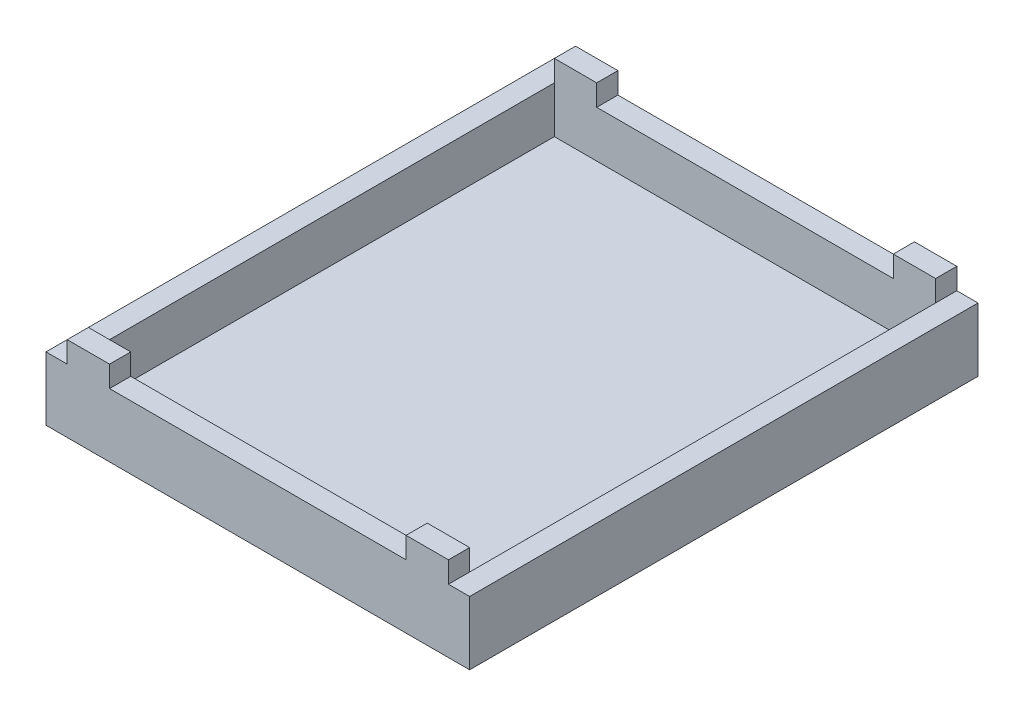
SolidWorks part; units mm, degrees
ref_plane "Front Plane" through (0, 0, 0) normal (0, 0, 1) x (1, 0, 0)
ref_plane "Top Plane" through (0, 0, 0) normal (0, 1, 0) x (1, 0, 0)
ref_plane "Right Plane" through (0, 0, 0) normal (1, 0, 0) x (0, 0, -1)
sketch "Sketch1" plane through (0, 0, 0) normal (0, 1, 0) x (1, 0, 0)
  line L1 (-50, 60) -> (50, 60)
  line L2 (-50, 60) -> (-50, -60)
  line L3 (-50, -60) -> (50, -60)
  line L4 (50, 60) -> (50, -60)
  line L5 (-50, 60) -> (50, -60) construction
  line L6 (-50, -60) -> (50, 60) construction
  point P0 (0, 0)
  dimension "D1" = 120
  dimension "D2" = 100
extrude "Boss-Extrude1" add sketch "Sketch1" along normal blind 20
sketch "Sketch2" plane through (0, 20, 0) normal (0, 1, 0) x (1, 0, 0)
  line L0 (50, 60) -> (-50, 60) construction
  line L1 (-45, 55) -> (45, 55)
  line L2 (-45, 55) -> (-45, -55)
  line L3 (-45, -55) -> (45, -55)
  line L4 (45, 55) -> (45, -55)
  line L5 (-50, 60) -> (-50, -60) construction
  dimension "D1" = 90
  dimension "D2" = 110
  dimension "D3" = 5
  dimension "D4" = 5
extrude "Cut-Extrude1" cut sketch "Sketch2" against normal blind 16
sketch "Sketch4" plane through (0, 0, 60) normal (0, 0, 1) x (1, 0, 0)
  line L0 (50, 20) -> (50, 0) construction
  line L1 (-50, 20) -> (-45, 20)
  line L2 (-50, 20) -> (-50, 15)
  line L3 (-50, 15) -> (-45, 15)
  line L4 (-45, 20) -> (-45, 15)
  line L5 (50, 20) -> (45, 20)
  line L6 (50, 20) -> (50, 15)
  line L7 (50, 15) -> (45, 15)
  line L8 (45, 20) -> (45, 15)
  line L9 (-50, 20) -> (50, 20) construction
  line L11 (-35, 20) -> (35, 20)
  line L12 (-35, 20) -> (-35, 15)
  line L13 (-35, 15) -> (35, 15)
  line L14 (35, 20) -> (35, 15)
  dimension "D1" = 5
  dimension "D2" = 5
  dimension "D3" = 5
  dimension "D4" = 5
  dimension "D5" = 70
  dimension "D6" = 5
  dimension "D7" = 10
extrude "Cut-Extrude2" cut sketch "Sketch4" against normal through all
